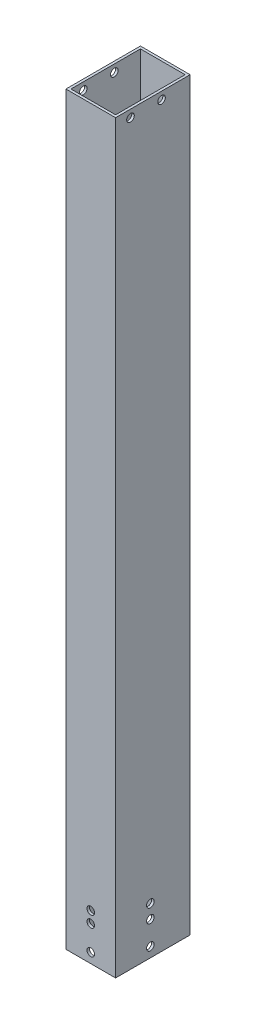
SolidWorks part; units mm, degrees
material "6063-T5"
ref_plane "前视基准面" through (0, 0, 0) normal (0, 0, 1) x (1, 0, 0)
ref_plane "上视基准面" through (0, 0, 0) normal (0, 1, 0) x (1, 0, 0)
ref_plane "右视基准面" through (0, 0, 0) normal (1, 0, 0) x (0, 0, -1)
other "Configuration Table"
sketch "草图1" plane through (0, 0, 0) normal (0, 1, 0) x (1, 0, 0)
  line L1 (-10, -15) -> (10, -15)
  line L2 (-10, -15) -> (-10, 15)
  line L3 (-10, 15) -> (10, 15)
  line L4 (10, -15) -> (10, 15)
  line L5 (-10, -15) -> (10, 15) construction
  line L6 (-10, 15) -> (10, -15) construction
  point P0 (0, 0)
  dimension "D1" = 20
  dimension "D2" = 30
extrude "凸台-拉伸1" add sketch "草图1" along normal mid plane 300
sketch "草图2" plane through (0, 150, 0) normal (0, 1, 0) x (1, 0, 0)
  line L8 (9, -14) -> (9, 14)
  line L9 (9, 14) -> (-9, 14)
  line L10 (-9, 14) -> (-9, -14)
  line L11 (-9, -14) -> (9, -14)
  line L12 (9, -14) -> (9, 14)
  line L13 (9, 14) -> (-9, 14)
  line L14 (-9, 14) -> (-9, -14)
  line L15 (-9, -14) -> (9, -14)
  dimension "D1" = 1
extrude "切除-拉伸1" cut sketch "草图2" against normal through all
sketch "草图3" plane through (10, 0, 0) normal (1, 0, 0) x (0, 0, -1)
  line L0 (-15, -150) -> (15, -150) construction
  line L1 (-15, 150) -> (-15, -150) construction
  circle A0 centre (-1, -146) radius 1.525
  dimension "D1" = 3.05
  dimension "D2" = 4
  dimension "D3" = 14
extrude "切除-拉伸2" cut sketch "草图3" against normal through all
sketch "草图4" plane through (0, 0, 15) normal (0, 0, 1) x (1, 0, 0)
  line L0 (-10, -150) -> (10, -150) construction
  circle A0 centre (0, -146) radius 1.525
  dimension "D1" = 3.05
  dimension "D2" = 4
extrude "切除-拉伸3" cut sketch "草图4" against normal through all
sketch "草图5" plane through (0, 0, 15) normal (0, 0, 1) x (1, 0, 0)
  line L1 (-10, -150) -> (10, -150) construction
  line L2 (10, 150) -> (10, -150) construction
  circle A0 centre (0, -136) radius 1.525
  dimension "D1" = 3.05
  dimension "D3" = 10
  dimension "D2" = 14
extrude "切除-拉伸4" cut sketch "草图5" against normal through all
sketch "草图6" plane through (10, 0, 0) normal (1, 0, 0) x (0, 0, -1)
  line L4 (-15, -150) -> (15, -150)
  line L5 (15, -150) -> (15, 150)
  line L6 (15, 150) -> (-15, 150)
  line L7 (-15, 150) -> (-15, -150)
  line L8 (-15, -150) -> (15, -150)
  line L9 (15, -150) -> (15, 150)
  line L10 (15, 150) -> (-15, 150)
  line L11 (-15, 150) -> (-15, -150)
  circle A0 centre (-1, -131) radius 1.525
  dimension "D2" = 3.05
  dimension "D3" = 16
  dimension "D4" = 19
  dimension "D1" = 0
extrude "切除-拉伸6" cut sketch "草图6" against normal through all flip side to cut
sketch "草图7" plane through (0, 150, 0) normal (0, 1, 0) x (1, 0, 0)
  circle A0 centre (0, 0) radius 5
  dimension "D1" = 10
sketch "草图9" plane through (0, 0, 15) normal (0, 0, 1) x (1, 0, 0)
  line L0 (-10, -150) -> (10, -150) construction
  line L1 (10, 150) -> (10, -150) construction
  circle A0 centre (0, -131.5) radius 1.525
  dimension "D1" = 3.05
  dimension "D3" = 10
  dimension "D2" = 18.5
extrude "切除-拉伸8" cut sketch "草图9" against normal up to next
sketch "草图10" plane through (10, 0, 0) normal (1, 0, 0) x (0, 0, -1)
  line L0 (15, 150) -> (15, -150) construction
  line L1 (-15, -150) -> (15, -150) construction
  circle A0 centre (-1, -136.5) radius 1.525
  dimension "D1" = 3.05
  dimension "D2" = 16
  dimension "D3" = 13.5
extrude "切除-拉伸9" cut sketch "草图10" against normal through all both
sketch "草图11" plane through (9, 0, 0) normal (-1, 0, 0) x (0, 0, 1)
  circle A0 centre (9, 147) radius 1.525
  circle A1 centre (-3.5, 147) radius 1.525
  dimension "D1" = 3.05
extrude "切除-拉伸10" cut sketch "草图11" against normal through all both and the other way through all
